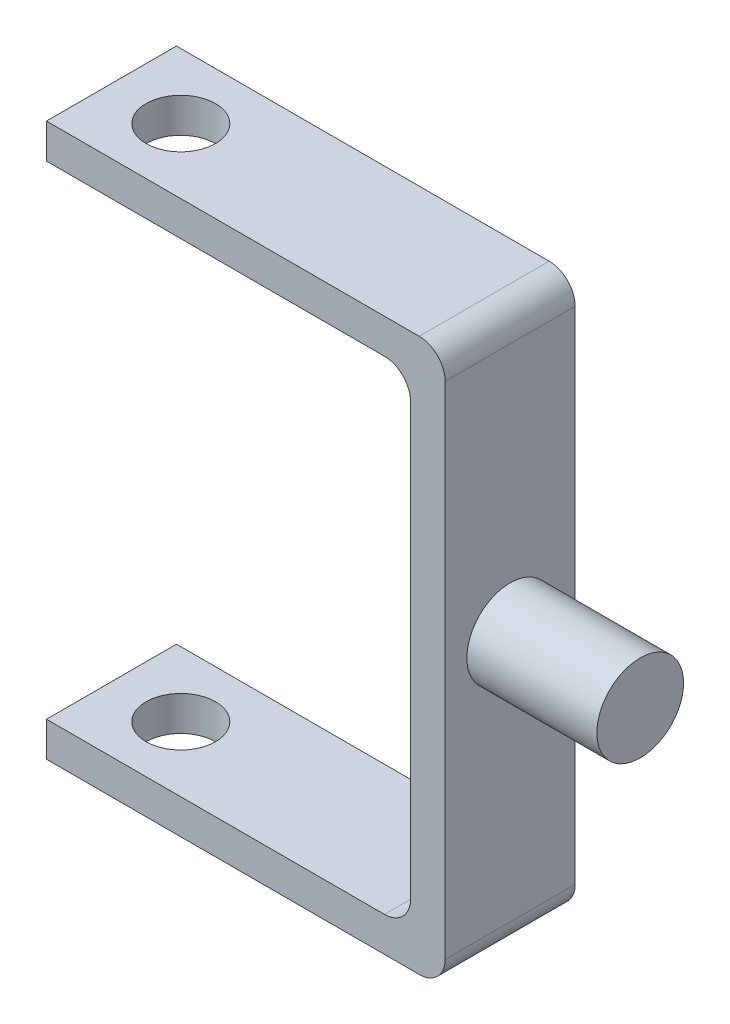
SolidWorks part; units mm, degrees
ref_plane "Front Plane" through (0, 0, 0) normal (0, 0, 1) x (1, 0, 0)
ref_plane "Top Plane" through (0, 0, 0) normal (0, 1, 0) x (1, 0, 0)
ref_plane "Right Plane" through (0, 0, 0) normal (1, 0, 0) x (0, 0, -1)
sketch "Sketch1" plane through (0, 0, 0) normal (0, 0, 1) x (1, 0, 0)
  line L0 (0, 0) -> (42, 0)
  line L1 (42, 0) -> (42, -55.7633)
  line L2 (42, -55.7633) -> (0, -55.7633)
  line L3 (0, 4) -> (46, 4)
  line L4 (46, 4) -> (46, -59.7633)
  line L5 (46, -59.7633) -> (0, -59.7633)
  line L6 (0, 4) -> (0, 0)
  line L7 (0, -55.7633) -> (0, -59.7633)
  dimension "D1" = 55.7633
  dimension "D2" = 42
  dimension "D3" = 4
extrude "Boss-Extrude1" add sketch "Sketch1" along normal blind 15
sketch "Sketch2" plane through (0, 4, 0) normal (0, 1, 0) x (1, 0, 0)
  line L0 (0, -15) -> (0, 0) construction
  circle A0 centre (8, -7.5) radius 4
  point P4 (0, -7.5)
  dimension "D1" = 8
  dimension "D2" = 8
extrude "Cut-Extrude1" cut sketch "Sketch2" against normal through all
fillet "Fillet1" radius 3 4 edges at (46, -59.7633, 7.5) (46, 4, 7.5) (42, -55.7633, 7.5) (42, 0, 7.5)
sketch "Sketch4" plane through (46, 0, 0) normal (1, 0, 0) x (0, 0, -1)
  line L0 (-15, -27.8816) -> (0, -27.8816) construction
  line L1 (-15, -56.7633) -> (-15, 1) construction
  line L2 (0, -56.7633) -> (0, 1) construction
  line L3 (-7.5, -56.7633) -> (-7.5, 1) construction
  line L4 (-15, -56.7633) -> (0, -56.7633) construction
  line L5 (0, 1) -> (-15, 1) construction
  circle A0 centre (-7.5, -27.8816) radius 5
  dimension "D1" = 10
extrude "Boss-Extrude2" add sketch "Sketch4" along normal blind 15
sketch "Sketch5" plane through (0, 0, 0) normal (0, 0, 1) x (1, 0, 0)
  line L0 (46, -27.8816) -> (61, -27.8816) construction
  line L1 (46, -32.8816) -> (46, -22.8816) construction
  line L2 (61, -32.8816) -> (61, -22.8816) construction
  circle A0 centre (56, -27.8816) radius 3
  dimension "D1" = 6
  dimension "D2" = 10
extrude "Cut-Extrude2" cut sketch "Sketch5" along normal blind 7
